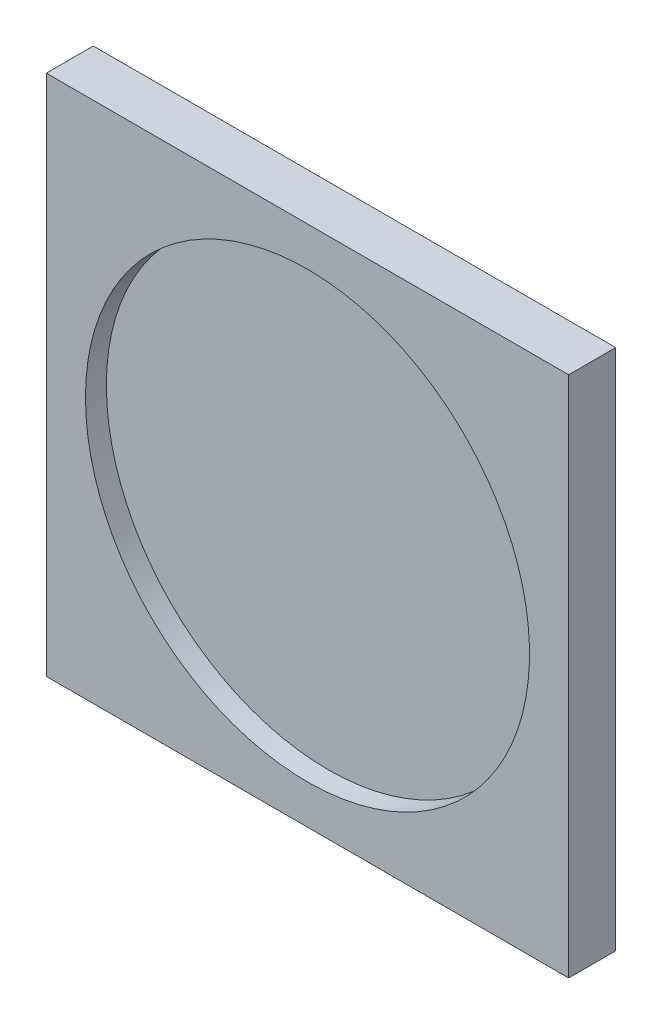
SolidWorks part; units mm, degrees
material "Oak"
ref_plane "Front Plane" through (0, 0, 0) normal (1, 0, 0) x (0, 1, 0)
ref_plane "Top Plane" through (0, 0, 0) normal (0, 0, 1) x (0, 1, 0)
ref_plane "Right Plane" through (0, 0, 0) normal (0, 1, 0) x (-1, 0, 0)
sketch "Sketch4" plane through (0, 0, 0) normal (1, 0, 0) x (0, 1, 0)
  line L1 (-50, 9) -> (50, 9)
  line L2 (-50, 9) -> (-50, 0)
  line L3 (-50, 0) -> (50, 0)
  line L4 (50, 9) -> (50, 0)
  dimension "D1" = 50
  dimension "D2" = 100
  dimension "D3" = 9
extrude "Boss-Extrude3" add sketch "Sketch4" along normal mid plane 100
sketch "Sketch5" plane through (0, 0, 9) normal (0, 0, 1) x (1, 0, 0)
  circle A0 centre (0, 0) radius 42.5
  dimension "D1" = 85
extrude "Cut-Extrude1" cut sketch "Sketch5" against normal blind 4 and the other way through all
